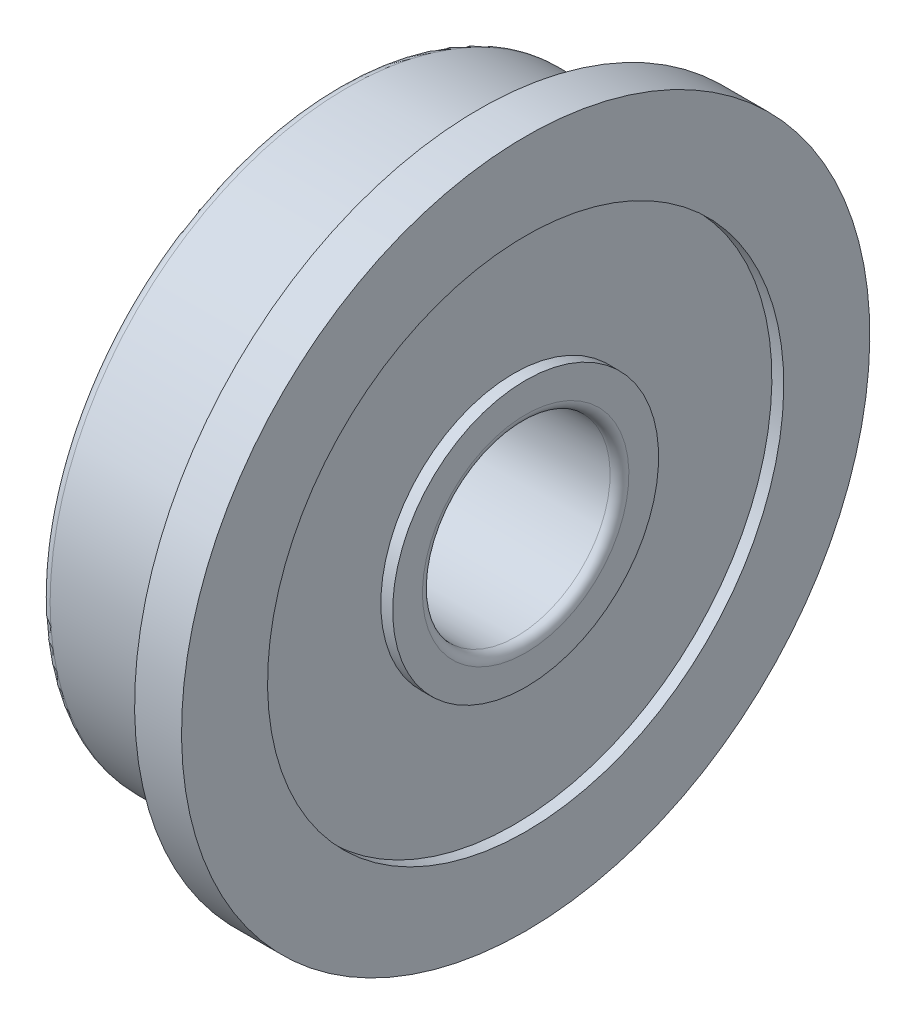
SolidWorks part; units mm, degrees
ref_plane "Front Plane" through (0, 0, 0) normal (0, 0, 1) x (1, 0, 0)
ref_plane "Top Plane" through (0, 0, 0) normal (0, 1, 0) x (1, 0, 0)
ref_plane "Right Plane" through (0, 0, 0) normal (1, 0, 0) x (0, 0, -1)
sketch "Sketch1" plane through (0, 0, 0) normal (0, 0, 1) x (1, 0, 0)
  line L0 (-4.5, 0) -> (1.5, 0) construction
  line L1 (0, 9.7) -> (0, 11)
  line L2 (0, 11) -> (1.5, 11)
  line L3 (1.5, 11) -> (1.5, 8.25)
  line L4 (1.5, 3) -> (-4.5, 3)
  line L5 (-4.5, 3) -> (-4.5, 4.25)
  line L6 (-4.5, 9.5) -> (-0.2, 9.5)
  line L7 (-4.5, 8.25) -> (-4.12, 8.25)
  line L8 (-4.12, 8.25) -> (-4.12, 4.25)
  line L9 (-4.12, 4.25) -> (-4.5, 4.25)
  line L10 (1.5, 8.25) -> (1.12, 8.25)
  line L11 (1.12, 8.25) -> (1.12, 4.25)
  line L12 (1.12, 4.25) -> (1.5, 4.25)
  line L13 (-4.5, 8.25) -> (-4.5, 9.5)
  line L14 (1.5, 4.25) -> (1.5, 3)
  arc A0 (-0.2, 9.5) -> (0, 9.7) centre (0, 9.5) ccw
  dimension "FIX_1" = 0.2
  dimension "D_s" = 6
  dimension "C" = 1.5
  dimension "MSM_2" = 8.5
  dimension "MSM_1" = 16.5
  dimension "D" = 19
  dimension "D1." = 22
  dimension "B" = 6
  dimension "MSM_3" = 0.38
revolve "Revolve1" add sketch "Sketch1" angle 360 about L0
fillet "Fillet1" radius 0.3 3 edges at (1.5, -3, 0) (-4.5, -3, 0) (-4.5, -9.5, 0)
